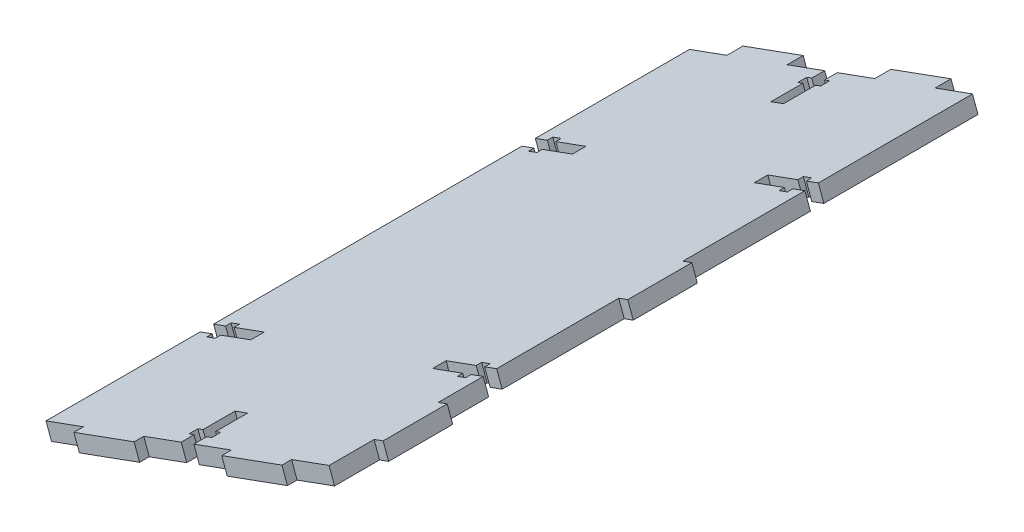
SolidWorks part; units mm, degrees
ref_plane "Front Plane" through (0, 0, 0) normal (0, 0, 1) x (1, 0, 0)
ref_plane "Top Plane" through (0, 0, 0) normal (0, 1, 0) x (1, 0, 0)
ref_plane "Right Plane" through (0, 0, 0) normal (1, 0, 0) x (0, 0, -1)
sketch "Sketch2" plane through (0, 0, 2) normal (0, 0, 1) x (1, 0, 0)
  line L12 (22.5342, 12.2858) -> (-69.5649, -21.2067) construction
  line L15 (107.8376, -222.285) -> (22.5342, 12.2858) construction
  line L17 (22.5342, 12.2858) -> (24.243, 7.5869)
  line L18 (22.5342, 12.2858) -> (-65.8058, -19.8396)
  line L19 (24.243, 7.5869) -> (-64.097, -24.5386)
  line L20 (-65.8058, -19.8396) -> (-64.097, -24.5386)
  line L24 (-55.0608, -49.3866) -> (-43.7827, -80.3995) construction
  point P8 (-207.8345, -76.1884)
  point P9 (66.9945, 22.6018)
  dimension "D1" = 5
extrude "Boss-Extrude1" add sketch "Sketch2" along normal up to surface (200.8 mm away)
sketch "Sketch4" plane through (0.3948, -1.0857, 0) normal (0.3418, -0.9398, 0) x (-0.9398, -0.3418, 0)
  line L0 (19.5238, -2) -> (23.7238, -2)
  line L1 (19.5238, -2) -> (19.5238, -6)
  line L2 (23.7238, -2) -> (23.7238, -6)
  line L3 (17.8238, -6) -> (19.5238, -6)
  line L4 (17.8238, -6) -> (17.8238, -8.8)
  line L5 (25.4238, -6) -> (25.4238, -8.8)
  line L6 (17.8238, -8.8) -> (19.5238, -8.8)
  line L7 (19.5238, -8.8) -> (19.5238, -18.8)
  line L8 (23.7238, -8.8) -> (23.7238, -18.8)
  line L9 (19.5238, -18.8) -> (23.7238, -18.8)
  line L10 (23.7238, -8.8) -> (25.4238, -8.8)
  line L11 (23.7238, -6) -> (25.4238, -6)
  line L14 (-25.3762, -54.3) -> (-25.3762, -50.1)
  line L25 (-25.3762, -2) -> (68.6238, -2) construction
  line L26 (23.7238, -202.8) -> (19.5238, -202.8)
  line L27 (23.7238, -202.8) -> (23.7238, -198.8)
  line L28 (21.6238, -18.8) -> (21.6238, -2) construction
  line L29 (19.5238, -202.8) -> (19.5238, -198.8)
  line L30 (25.4238, -198.8) -> (23.7238, -198.8)
  line L31 (25.4238, -198.8) -> (25.4238, -196)
  line L32 (17.8238, -198.8) -> (17.8238, -196)
  line L33 (25.4238, -196) -> (23.7238, -196)
  line L34 (23.7238, -196) -> (23.7238, -186)
  line L35 (19.5238, -196) -> (19.5238, -186)
  line L36 (23.7238, -186) -> (19.5238, -186)
  line L37 (19.5238, -196) -> (17.8238, -196)
  line L38 (19.5238, -198.8) -> (17.8238, -198.8)
  line L39 (21.6238, -186) -> (21.6238, -202.8) construction
  line L40 (-25.3762, -202.8) -> (68.6238, -202.8) construction
  line L41 (-25.3762, -54.3) -> (-21.3762, -54.3)
  line L42 (-25.3762, -50.1) -> (-21.3762, -50.1)
  line L43 (-21.3762, -56) -> (-21.3762, -54.3)
  line L44 (-21.3762, -56) -> (-18.5762, -56)
  line L45 (-21.3762, -48.4) -> (-18.5762, -48.4)
  line L46 (-18.5762, -56) -> (-18.5762, -54.3)
  line L47 (-18.5762, -54.3) -> (-8.5762, -54.3)
  line L48 (-18.5762, -50.1) -> (-8.5762, -50.1)
  line L49 (-8.5762, -54.3) -> (-8.5762, -50.1)
  line L50 (-18.5762, -50.1) -> (-18.5762, -48.4)
  line L51 (-21.3762, -50.1) -> (-21.3762, -48.4)
  line L52 (-8.5762, -52.2) -> (-25.3762, -52.2) construction
  line L55 (-25.3762, -202.8) -> (-25.3762, -2) construction
  line L56 (-25.3762, -2) -> (-25.3762, -102.4) construction
  line L57 (-25.3762, -102.4) -> (68.6238, -102.4) construction
  line L58 (-8.5762, -152.6) -> (-25.3762, -152.6) construction
  line L59 (-21.3762, -154.7) -> (-21.3762, -156.4)
  line L60 (-18.5762, -154.7) -> (-18.5762, -156.4)
  line L61 (-8.5762, -150.5) -> (-8.5762, -154.7)
  line L62 (-18.5762, -154.7) -> (-8.5762, -154.7)
  line L63 (-18.5762, -150.5) -> (-8.5762, -150.5)
  line L64 (-18.5762, -148.8) -> (-18.5762, -150.5)
  line L65 (-21.3762, -156.4) -> (-18.5762, -156.4)
  line L66 (-21.3762, -148.8) -> (-18.5762, -148.8)
  line L67 (-21.3762, -148.8) -> (-21.3762, -150.5)
  line L68 (-25.3762, -154.7) -> (-21.3762, -154.7)
  line L69 (-25.3762, -150.5) -> (-21.3762, -150.5)
  line L70 (-25.3762, -150.5) -> (-25.3762, -154.7)
  line L76 (68.6238, -202.8) -> (68.6238, -2) construction
  line L77 (21.6238, -171.4513) -> (21.6238, -40.1199) construction
  line L78 (51.8238, -152.6) -> (68.6238, -152.6) construction
  line L87 (68.6238, -2) -> (68.6238, -102.4) construction
  line L88 (51.8238, -52.2) -> (68.6238, -52.2) construction
  line L89 (68.6238, -150.5) -> (68.6238, -154.7)
  line L90 (68.6238, -150.5) -> (64.6238, -150.5)
  line L91 (68.6238, -154.7) -> (64.6238, -154.7)
  line L92 (64.6238, -148.8) -> (64.6238, -150.5)
  line L93 (64.6238, -148.8) -> (61.8238, -148.8)
  line L94 (64.6238, -156.4) -> (61.8238, -156.4)
  line L95 (61.8238, -148.8) -> (61.8238, -150.5)
  line L96 (61.8238, -150.5) -> (51.8238, -150.5)
  line L97 (61.8238, -154.7) -> (51.8238, -154.7)
  line L98 (51.8238, -150.5) -> (51.8238, -154.7)
  line L99 (61.8238, -154.7) -> (61.8238, -156.4)
  line L100 (64.6238, -154.7) -> (64.6238, -156.4)
  line L101 (64.6238, -50.1) -> (64.6238, -48.4)
  line L102 (61.8238, -50.1) -> (61.8238, -48.4)
  line L103 (51.8238, -54.3) -> (51.8238, -50.1)
  line L104 (61.8238, -50.1) -> (51.8238, -50.1)
  line L105 (61.8238, -54.3) -> (51.8238, -54.3)
  line L106 (61.8238, -56) -> (61.8238, -54.3)
  line L107 (64.6238, -48.4) -> (61.8238, -48.4)
  line L108 (64.6238, -56) -> (61.8238, -56)
  line L109 (64.6238, -56) -> (64.6238, -54.3)
  line L110 (68.6238, -50.1) -> (64.6238, -50.1)
  line L111 (68.6238, -54.3) -> (64.6238, -54.3)
  line L112 (68.6238, -54.3) -> (68.6238, -50.1)
  point P70 (21.6238, -102.4)
  dimension "D1" = 4.2
  dimension "D2" = 1.7
  dimension "D3" = 1.7
  dimension "D4" = 2.8
  dimension "D5" = 10
  dimension "D6" = 4
  dimension "D7" = 4.2
  dimension "D8" = 1.7
  dimension "D9" = 1.7
  dimension "D10" = 2.8
  dimension "D11" = 10
  dimension "D12" = 4
  dimension "D13" = 4.2
  dimension "D14" = 1.7
  dimension "D15" = 1.7
  dimension "D16" = 2.8
  dimension "D17" = 10
  dimension "D18" = 4
extrude "Cut-Extrude3" cut sketch "Sketch4" against normal through all
sketch "Sketch5" plane through (0.3948, -1.0857, 0) normal (0.3418, -0.9398, 0) x (0.9398, 0.3418, 0)
  line L0 (-36.1738, 202.8) -> (-56.1738, 202.8)
  line L1 (-36.1738, 202.8) -> (-36.1738, 205.8)
  line L2 (-56.1738, 202.8) -> (-56.1738, 205.8)
  line L3 (-36.1738, 205.8) -> (-56.1738, 205.8)
  line L4 (-68.6238, 202.8) -> (-23.7238, 202.8) construction
  line L5 (12.9262, 202.8) -> (-7.0738, 202.8)
  line L6 (12.9262, 202.8) -> (12.9262, 205.8)
  line L7 (-7.0738, 202.8) -> (-7.0738, 205.8)
  line L8 (12.9262, 205.8) -> (-7.0738, 205.8)
  line L9 (-19.5238, 202.8) -> (25.3762, 202.8) construction
  line L10 (25.3762, 92.4) -> (25.3762, 112.4)
  line L11 (25.3762, 92.4) -> (28.3762, 92.4)
  line L12 (25.3762, 112.4) -> (28.3762, 112.4)
  line L13 (28.3762, 92.4) -> (28.3762, 112.4)
  line L14 (25.3762, 54.3) -> (25.3762, 150.5) construction
  line L15 (25.3762, 188.75) -> (25.3762, 168.75)
  line L16 (25.3762, 188.75) -> (28.3762, 188.75)
  line L17 (25.3762, 168.75) -> (28.3762, 168.75)
  line L18 (28.3762, 188.75) -> (28.3762, 168.75)
  line L19 (25.3762, 154.7) -> (25.3762, 202.8) construction
  line L20 (25.3762, 92.4) -> (25.3762, 112.4)
  line L24 (25.3762, 54.3) -> (25.3762, 150.5) construction
  line L25 (-56.1738, 2) -> (-36.1738, 2)
  line L26 (-56.1738, 2) -> (-56.1738, -3)
  line L27 (-36.1738, 2) -> (-36.1738, -3)
  line L28 (-56.1738, -3) -> (-36.1738, -3)
  line L29 (-68.6238, 2) -> (-23.7238, 2) construction
  line L30 (-7.0738, 2) -> (12.9262, 2)
  line L31 (-7.0738, 2) -> (-7.0738, -3)
  line L32 (12.9262, 2) -> (12.9262, -3)
  line L33 (-7.0738, -3) -> (12.9262, -3)
  line L34 (-19.5238, 2) -> (25.3762, 2) construction
  line L35 (25.3762, 205.8) -> (-124.6238, 205.8) construction
  point P10 (-46.1738, 202.8)
  point P11 (2.9262, 202.8)
  point P16 (25.3762, 102.4)
  point P17 (3.0867, 112.4)
  point P23 (25.3762, 178.75)
  point P31 (25.3762, 102.4)
  point P39 (-46.1738, 2)
  point P49 (2.9262, 2)
  dimension "D2" = 20
  dimension "D4" = 20
  dimension "D5" = 3
  dimension "D6" = 20
  dimension "D7" = 3
  dimension "D8" = 20
  dimension "D11" = 5
  dimension "D12" = 20
  dimension "D13" = 5
  dimension "D14" = 20
extrude "Boss-Extrude2" add sketch "Sketch5" against normal blind 5 contours L31 L33 L32 L30 | L26 L28 L27 L25 | L11 L13 L12 L10 | L18 L16 L15 L17 | L6 L8 L7 L5 | L1 L3 L2 L0
